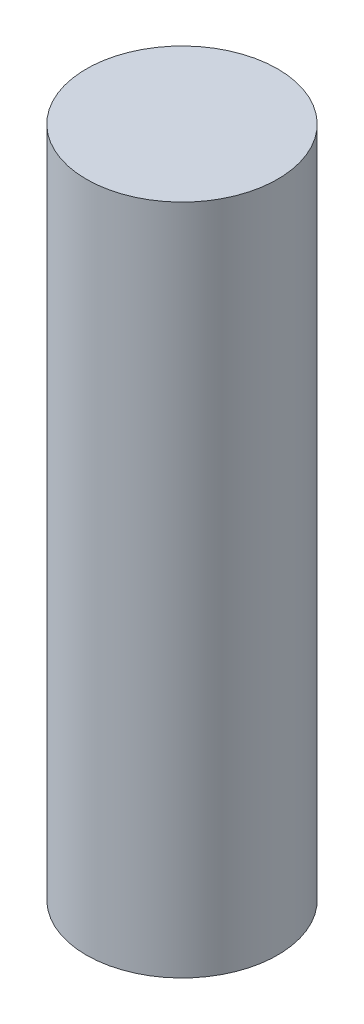
SolidWorks part; units mm, degrees
ref_plane "Front Plane" through (0, 0, 0) normal (0, 0, 1) x (1, 0, 0)
ref_plane "Top Plane" through (0, 0, 0) normal (0, 1, 0) x (1, 0, 0)
ref_plane "Right Plane" through (0, 0, 0) normal (1, 0, 0) x (0, 0, -1)
sketch "Sketch1" plane through (0, 0, 0) normal (0, 1, 0) x (1, 0, 0)
  circle A0 centre (0, 0) radius 9.25
  dimension "D1" = 18.5
extrude "Boss-Extrude1" add sketch "Sketch1" along normal blind 65
